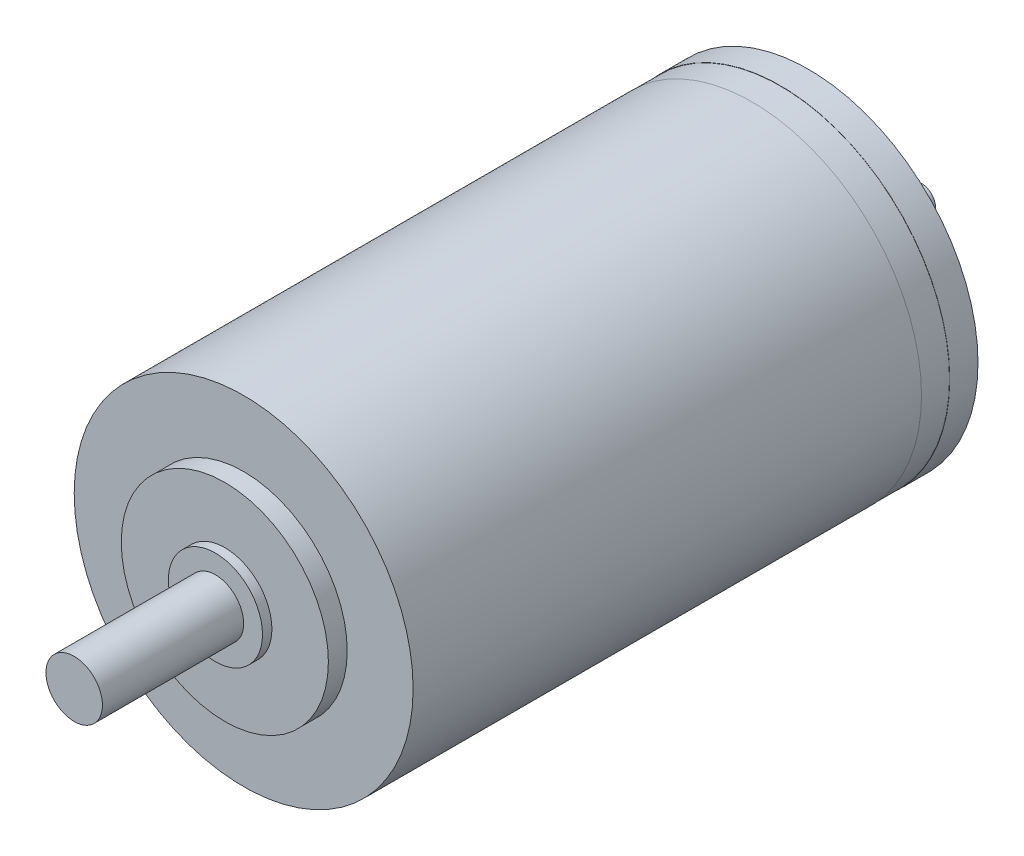
SolidWorks part; units mm, degrees
material "黃銅"
ref_plane "前基準面" through (0, 0, 0) normal (0, 0, 1) x (1, 0, 0)
ref_plane "上基準面" through (0, 0, 0) normal (0, 1, 0) x (1, 0, 0)
ref_plane "右基準面" through (0, 0, 0) normal (1, 0, 0) x (0, 0, -1)
sketch "草圖1" plane through (0, 0, 0) normal (0, 0, 1) x (1, 0, 0)
  circle A0 centre (0, 0) radius 17.975
  dimension "D1" = 35.95
extrude "填料-伸長1" add sketch "草圖1" along normal blind 3
sketch "草圖2" plane through (0, 0, 3) normal (0, 0, 1) x (1, 0, 0)
  circle A0 centre (0, 0) radius 18
  dimension "D1" = 36
extrude "填料-伸長2" add sketch "草圖2" along normal blind 50
sketch "草圖3" plane through (0, 0, 53) normal (0, 0, 1) x (1, 0, 0)
  circle A0 centre (0, 0) radius 18
extrude "填料-伸長3" add sketch "草圖3" along normal blind 4
sketch "草圖4" plane through (0, 0, 57) normal (0, 0, 1) x (1, 0, 0)
  circle A0 centre (0, 0) radius 11
  dimension "D1" = 22
extrude "填料-伸長4" add sketch "草圖4" along normal blind 2
sketch "草圖5" plane through (0, 0, 59) normal (0, 0, 1) x (1, 0, 0)
  circle A0 centre (0, 0) radius 5
  dimension "D1" = 10
extrude "填料-伸長6" add sketch "草圖5" along normal blind 1
sketch "草圖6" plane through (0, 0, 60) normal (0, 0, 1) x (1, 0, 0)
  circle A0 centre (0, 0) radius 3
  dimension "D1" = 6
extrude "填料-伸長7" add sketch "草圖6" along normal blind 15
sketch "草圖8" plane through (0, 0, 0) normal (0, 0, -1) x (-1, 0, 0)
  circle A0 centre (0, 0) radius 18
  dimension "D1" = 36
extrude "填料-伸長9" add sketch "草圖8" along normal blind 3
sketch "草圖9" plane through (0, 0, -3) normal (0, 0, -1) x (-1, 0, 0)
  circle A0 centre (0, 0) radius 5
  dimension "D1" = 10
extrude "填料-伸長10" add sketch "草圖9" along normal blind 2
sketch "草圖10" plane through (0, 0, -5) normal (0, 0, -1) x (-1, 0, 0)
  circle A0 centre (0, 0) radius 1.5
  dimension "D1" = 3
extrude "填料-伸長11" add sketch "草圖10" along normal blind 10
